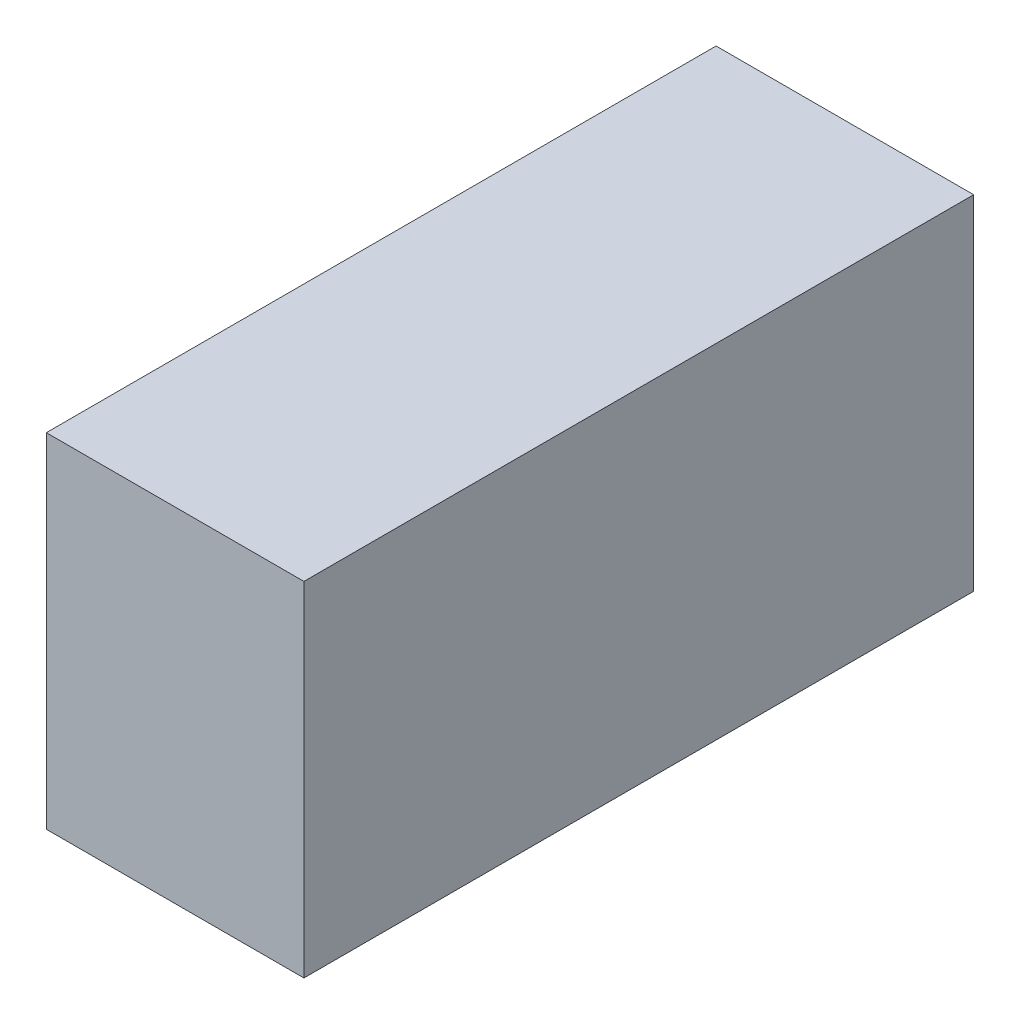
SolidWorks part; units mm, degrees
ref_plane "Front Plane" through (0, 0, 0) normal (0, 0, 1) x (1, 0, 0)
ref_plane "Top Plane" through (0, 0, 0) normal (0, 1, 0) x (1, 0, 0)
ref_plane "Right Plane" through (0, 0, 0) normal (1, 0, 0) x (0, 0, -1)
sketch "Sketch1" plane through (0, 0, 0) normal (1, 0, 0) x (0, 0, -1)
  line L0 (0.3175, 6.35) -> (0.3175, -6.35) construction
  line L1 (12.3825, -6.35) -> (-12.3825, -6.35) construction
  line L2 (12.3825, -6.35) -> (12.3825, 6.35) construction
  line L3 (12.3825, 6.35) -> (-12.3825, 6.35) construction
  line L4 (-12.3825, -6.35) -> (-12.3825, 6.35) construction
  line L5 (12.3825, -6.35) -> (-12.3825, 6.35) construction
  line L6 (12.3825, 6.35) -> (-12.3825, -6.35) construction
  line L7 (-0.3175, 6.35) -> (-0.3175, -6.35) construction
  point P0 (0, 0)
  dimension "Length" = 24.765
  dimension "Width" = 12.7
  dimension "D1" = 12.7
  dimension "D2" = 12.7
sketch "Sketch2" plane through (0, 0, 0) normal (0, 0, 1) x (1, 0, 0)
  line L0 (-4.7625, 6.35) -> (4.7625, 6.35) construction
  point P3 (0, 6.35)
  dimension "Thickness" = 9.525
sketch "Sketch3" plane through (0, 0, 0) normal (0, 0, 1) x (1, 0, 0)
  line L1 (-4.7625, 6.35) -> (4.7625, 6.35)
  line L2 (-4.7625, 6.35) -> (-4.7625, -6.35)
  line L3 (-4.7625, -6.35) -> (4.7625, -6.35)
  line L4 (4.7625, 6.35) -> (4.7625, -6.35)
  line L5 (-4.7625, 6.35) -> (4.7625, -6.35) construction
  line L6 (-4.7625, -6.35) -> (4.7625, 6.35) construction
  point P4 (0, 0)
extrude "Boss-Extrude1" add sketch "Sketch3" along normal up to vertex (12.3825 mm away) and the other way up to vertex (12.3825 mm away) up to point (0, 6.35, 12.3825) other way up to point (0, 6.35, -12.3825)
equation "\"D2@Sketch1\"=\"D1@Sketch1\""
